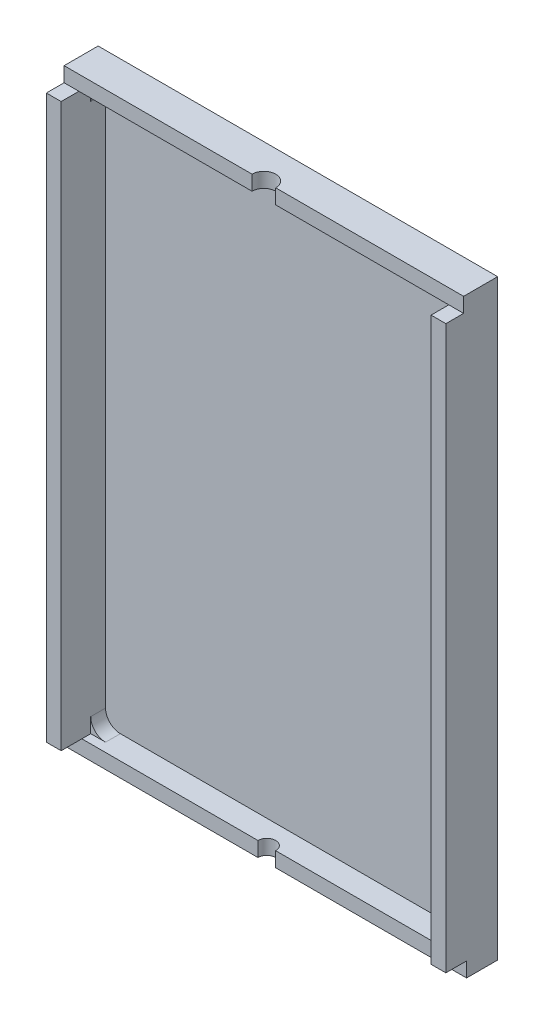
SolidWorks part; units mm, degrees
ref_plane "Front" through (0, 0, 0) normal (0, 0, 1) x (1, 0, 0)
ref_plane "Top" through (0, 0, 0) normal (0, 1, 0) x (1, 0, 0)
ref_plane "Right" through (0, 0, 0) normal (1, 0, 0) x (0, 0, -1)
sketch "草图13" plane through (0, 0, 0) normal (0, 0, 1) x (1, 0, 0)
  line L1 (0, 0) -> (27, 0)
  line L2 (0, 0) -> (0, 40)
  line L3 (0, 40) -> (27, 40)
  line L4 (27, 0) -> (27, 40)
  dimension "D1" = 40
  dimension "D2" = 27
extrude "凸台-拉伸11" add sketch "草图13" along normal blind 0.5
sketch "草图14" plane through (0, 0, 0.5) normal (0, 0, 1) x (1, 0, 0)
  line L1 (0, 0) -> (27, 0)
  line L2 (0, 0) -> (0, 40)
  line L3 (0, 40) -> (27, 40)
  line L4 (27, 0) -> (27, 40)
  line L5 (2, 1) -> (25, 1)
  line L6 (1, 2) -> (1, 38)
  line L7 (2, 39) -> (25, 39)
  line L8 (26, 2) -> (26, 38)
  arc A0 (26, 38) -> (25, 39) centre (25, 38) ccw
  arc A1 (2, 39) -> (1, 38) centre (2, 38) ccw
  arc A3 (25, 1) -> (26, 2) centre (25, 2) ccw
  arc A4 (1, 2) -> (2, 1) centre (2, 2) ccw
  dimension "D1" = 1
  dimension "D2" = 1
  dimension "D3" = 1
  dimension "D4" = 1
extrude "凸台-拉伸14" add sketch "草图14" along normal blind 1
sketch "草图17" plane through (0, 0, 1.5) normal (0, 0, 1) x (1, 0, 0)
  line L0 (27, 0) -> (27, 40) construction
  line L1 (0, 40) -> (27, 40)
  line L2 (0, 40) -> (0, 39)
  line L3 (0, 39) -> (27, 39)
  line L4 (27, 40) -> (27, 39)
extrude "凸台-拉伸15" add sketch "草图17" along normal blind 0.8
sketch "草图18" plane through (0, 39, 0) normal (0, -1, 0) x (1, 0, 0)
  line L0 (0, 2.3) -> (27, 2.3) construction
  circle A0 centre (13.5, 2.3) radius 0.8
  dimension "D1" = 1.6
extrude "切除-拉伸4" cut sketch "草图18" against normal through all
sketch "草图22" plane through (0, 0, 1.5) normal (0, 0, 1) x (1, 0, 0)
  line L0 (27, 0) -> (27, 39) construction
  line L1 (0, 0) -> (27, 0)
  line L2 (0, 0) -> (0, 1)
  line L3 (0, 1) -> (27, 1)
  line L4 (27, 0) -> (27, 1)
extrude "凸台-拉伸18" add sketch "草图22" along normal blind 0.6
sketch "草图23" plane through (0, 0, 0) normal (0, -1, 0) x (1, 0, 0)
  line L0 (0, 2.1) -> (27, 2.1) construction
  circle A0 centre (13.5, 2.1) radius 0.6
  dimension "D1" = 1.2
extrude "切除-拉伸6" cut sketch "草图23" against normal blind 1
sketch "草图24" plane through (0, 0, 1.5) normal (0, 0, 1) x (1, 0, 0)
  line L0 (25, 39) -> (27, 39) construction
  line L1 (27, 1) -> (26, 1)
  line L2 (27, 1) -> (27, 39)
  line L3 (27, 39) -> (26, 39)
  line L4 (26, 1) -> (26, 39)
extrude "凸台-拉伸19" add sketch "草图24" along normal blind 2
sketch "草图25" plane through (0, 0, 1.5) normal (0, 0, 1) x (1, 0, 0)
  line L0 (0, 39) -> (2, 39) construction
  line L1 (0, 1) -> (1, 1)
  line L2 (0, 1) -> (0, 39)
  line L3 (0, 39) -> (1, 39)
  line L4 (1, 1) -> (1, 39)
extrude "凸台-拉伸20" add sketch "草图25" along normal blind 2
